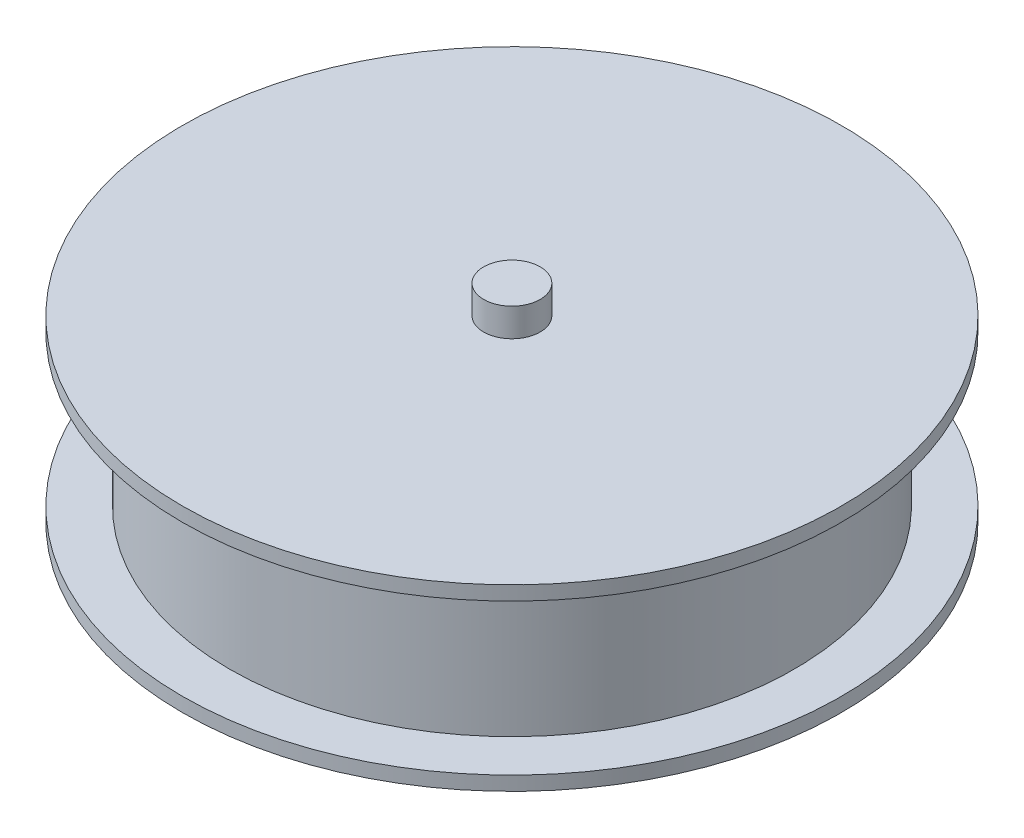
SolidWorks part; units mm, degrees
ref_plane "Front Plane" through (0, 0, 0) normal (0, 0, 1) x (1, 0, 0)
ref_plane "Top Plane" through (0, 0, 0) normal (0, 1, 0) x (1, 0, 0)
ref_plane "Right Plane" through (0, 0, 0) normal (1, 0, 0) x (0, 0, -1)
sketch "Sketch1" plane through (0, 0, 0) normal (0, 1, 0) x (1, 0, 0)
  circle A0 centre (0, 0) radius 35
  dimension "D1" = 70
extrude "Boss-Extrude1" add sketch "Sketch1" along normal blind 1.5
sketch "Sketch2" plane through (0, 1.5, 0) normal (0, 1, 0) x (1, 0, 0)
  circle A0 centre (0, 0) radius 30
  dimension "D1" = 60
extrude "Boss-Extrude3" add sketch "Sketch2" along normal blind 8 contours A0
mirror "Mirror1" about plane through (0, 9.5, 0) normal (0, 1, 0) of bodies 108
sketch "Sketch3" plane through (0, 19, 0) normal (0, 1, 0) x (1, 0, 0)
  circle A0 centre (0, 0) radius 3
  dimension "D1" = 6
extrude "Cut-Extrude1" cut sketch "Sketch3" against normal blind 80
sketch "Sketch6" plane through (0, 19, 0) normal (0, 1, 0) x (1, 0, 0)
  circle A0 centre (0, 0) radius 3
extrude "Boss-Extrude5" add sketch "Sketch6" along normal blind 3 separate body
